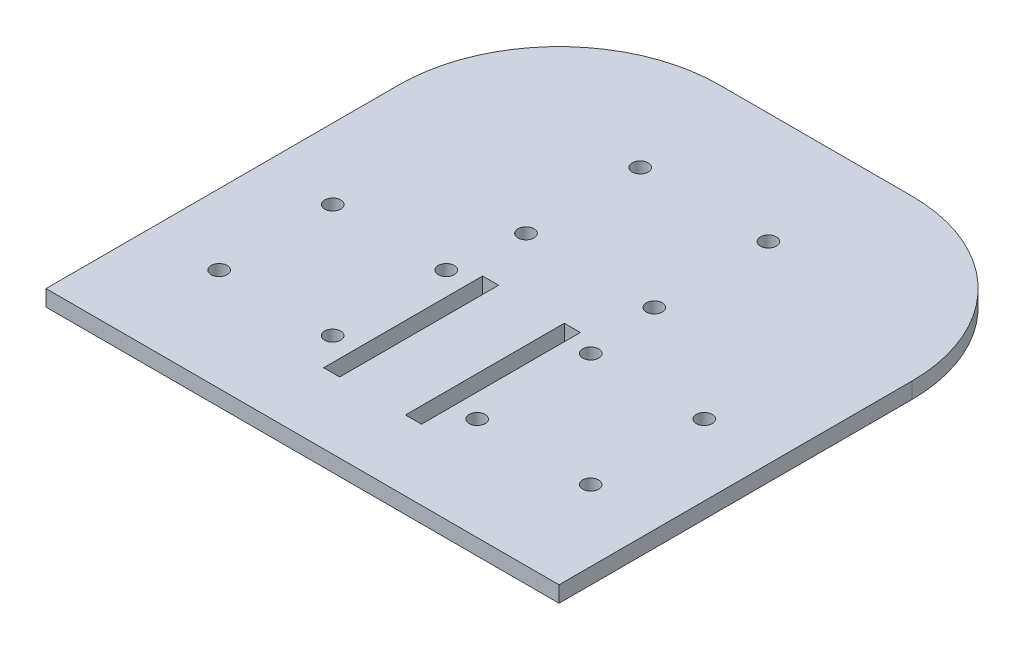
SolidWorks part; units mm, degrees
material "Acrylic (Medium-high impact)"
ref_plane "Front Plane" through (0, 0, 0) normal (0, 0, 1) x (1, 0, 0)
ref_plane "Top Plane" through (0, 0, 0) normal (0, 1, 0) x (1, 0, 0)
ref_plane "Right Plane" through (0, 0, 0) normal (1, 0, 0) x (0, 0, -1)
sketch "Sketch1" plane through (0, 0, 0) normal (0, 1, 0) x (1, 0, 0)
  line L1 (-101.6, -101.6) -> (101.6, -101.6)
  line L2 (-101.6, -101.6) -> (-101.6, 101.6)
  line L3 (-101.6, 101.6) -> (101.6, 101.6)
  line L4 (101.6, -101.6) -> (101.6, 101.6)
  line L5 (-101.6, -101.6) -> (101.6, 101.6) construction
  line L6 (-101.6, 101.6) -> (101.6, -101.6) construction
  point P0 (0, 0)
  dimension "D1" = 203.2
  dimension "D2" = 203.2
extrude "Boss-Extrude1" add sketch "Sketch1" along normal blind 6.35
sketch "Sketch2" plane through (0, 6.35, 0) normal (0, 1, 0) x (1, 0, 0)
  line L9 (101.6, 38.1) -> (101.6, 101.6)
  line L10 (101.6, 101.6) -> (38.1, 101.6)
  line L11 (-38.1, 101.6) -> (-101.6, 101.6)
  line L12 (-101.6, 101.6) -> (-101.6, 38.1)
  arc A2 (101.6, 38.1) -> (38.1, 101.6) centre (38.1, 38.1) ccw
  arc A3 (-101.6, 38.1) -> (-38.1, 101.6) centre (-38.1, 38.1) cw
extrude "Cut-Extrude1" cut sketch "Sketch2" against normal through all
sketch "Sketch9" plane through (0, 0, 0) normal (0, -1, 0) x (1, 0, 0)
  line L0 (-38.766, 10.8317) -> (-38.512, 10.8317) construction
  line L1 (-38.766, 73.756) -> (-38.512, 73.756) construction
  line L2 (38.5855, 10.8317) -> (38.3315, 10.8317) construction
  line L3 (-38.512, 10.8317) -> (-32.162, 10.8317)
  line L4 (-38.512, 10.8317) -> (-38.512, 73.756)
  line L5 (-38.512, 73.756) -> (-32.162, 73.756)
  line L6 (-32.162, 10.8317) -> (-32.162, 73.756)
  line L7 (38.5855, 73.756) -> (38.3315, 73.756) construction
  line L8 (-101.6, 101.6) -> (101.6, 101.6) construction
  line L13 (38.3315, 73.756) -> (31.9815, 73.756)
  line L14 (38.3315, 73.756) -> (38.3315, 10.8317)
  line L15 (38.3315, 10.8317) -> (31.9815, 10.8317)
  line L16 (31.9815, 73.756) -> (31.9815, 10.8317)
  line L17 (-101.6, -38.1) -> (-101.6, 101.6) construction
  circle A0 centre (-47.7463, 64.7757) radius 3.175 construction
  circle A1 centre (-47.7463, 19.812) radius 3.175 construction
  circle A2 centre (-92.71, 19.812) radius 3.175 construction
  circle A3 centre (-92.71, 64.7757) radius 3.175 construction
  circle A4 centre (-25.4903, -11.842) radius 3.175 construction
  circle A5 centre (25.3097, -11.842) radius 3.175 construction
  circle A6 centre (25.3097, -57.054) radius 3.175 construction
  circle A7 centre (-25.4903, -57.054) radius 3.175 construction
  circle A8 centre (47.5658, 19.812) radius 3.175 construction
  circle A9 centre (92.5295, 19.812) radius 3.175 construction
  circle A10 centre (92.5295, 64.7757) radius 3.175 construction
  circle A11 centre (47.5658, 64.7757) radius 3.175 construction
  circle A12 centre (-25.4903, -31.4508) radius 3.175
  circle A13 centre (25.3097, -31.4508) radius 3.175
  circle A14 centre (-25.4903, -76.6628) radius 3.175
  circle A15 centre (25.3097, -76.6628) radius 3.175
  circle A16 centre (-47.7463, 80.0157) radius 3.175
  circle A17 centre (-92.71, 80.0157) radius 3.175
  circle A18 centre (-47.7463, 35.052) radius 3.16
  circle A19 centre (-92.71, 35.052) radius 3.2058
  circle A20 centre (47.5658, 80.0157) radius 3.175
  circle A21 centre (92.5295, 80.0157) radius 3.175
  circle A22 centre (47.5658, 35.052) radius 3.175
  circle A23 centre (92.5295, 35.052) radius 3.175
  dimension "D22" = 6.35
  dimension "D23" = 6.35
  dimension "D24" = 6.35
  dimension "D26" = 6.35
  dimension "D27" = 6.35
  dimension "D28" = 6.35
  dimension "D29" = 6.35
  dimension "D30" = 6.35
  dimension "D31" = 6.35
  dimension "D32" = 6.35
  dimension "D33" = 6.35
  dimension "D36" = 19.6088
  dimension "D37" = 19.6088
  dimension "D38" = 19.6088
  dimension "D40" = 15.24
  dimension "D41" = 15.24
  dimension "D44" = 6.35
  dimension "D45" = 6.35
  dimension "D46" = 6.35
  dimension "D47" = 6.35
  dimension "D48" = 6.35
  dimension "D49" = 6.35
  dimension "D50" = 6.4115
  dimension "D51" = 6.32
  dimension "D1" = 0.254
  dimension "D2" = 6.35
  dimension "D4" = 44.9637
  dimension "D5" = 63.5883
  dimension "D6" = 44.9637
  dimension "D7" = 54.6863
  dimension "D8" = 53.944
  dimension "D9" = 60.548
  dimension "D10" = 135.86
  dimension "D11" = 141.9453
  dimension "D12" = 125.0145
  dimension "D13" = 131.2955
  dimension "D14" = 140.2758
  dimension "D15" = 185.2395
  dimension "D16" = 190.6185
  dimension "D17" = 122.191
  dimension "D18" = 74.2999
  dimension "D19" = 102.1121
  dimension "D20" = 140.8441
  dimension "D21" = 3.175
  dimension "D25" = 147.3059
  dimension "D34" = 8.89
  dimension "D35" = 81.788
  dimension "D39" = 19.6088
  dimension "D42" = 15.24
  dimension "D43" = 15.24
  dimension "D52" = 15.24
  dimension "D53" = 15.24
  dimension "D54" = 15.24
  dimension "D55" = 15.24
extrude "Cut-Extrude2" [suppressed] cut sketch "Sketch9" against normal through all
sketch "Sketch10" plane through (0, 0, 0) normal (0, -1, 0) x (1, 0, 0)
  line L0 (-19.462, 10.8317) -> (-13.112, 10.8317)
  line L1 (-13.112, 10.8317) -> (-13.112, 73.756)
  line L2 (-13.112, 73.756) -> (-19.462, 73.756)
  line L3 (-19.462, 73.756) -> (-19.462, 10.8317)
  line L4 (-38.512, 10.8317) -> (-32.162, 10.8317)
  line L5 (-32.162, 10.8317) -> (-32.162, 73.756)
  line L6 (-32.162, 73.756) -> (-38.512, 73.756)
  line L7 (-38.512, 73.756) -> (-38.512, 10.8317)
  line L8 (-38.512, 10.8317) -> (-32.162, 10.8317) construction
  line L9 (-32.162, 10.8317) -> (-32.162, 73.756) construction
  line L10 (-32.162, 73.756) -> (-38.512, 73.756) construction
  line L11 (-38.512, 73.756) -> (-38.512, 10.8317) construction
  line L12 (38.3315, 73.756) -> (31.9815, 73.756)
  line L13 (31.9815, 73.756) -> (31.9815, 10.8317)
  line L14 (31.9815, 10.8317) -> (38.3315, 10.8317)
  line L15 (38.3315, 10.8317) -> (38.3315, 73.756)
  line L16 (38.3315, 73.756) -> (31.9815, 73.756) construction
  line L17 (31.9815, 73.756) -> (31.9815, 10.8317) construction
  line L18 (31.9815, 10.8317) -> (38.3315, 10.8317) construction
  line L19 (38.3315, 10.8317) -> (38.3315, 73.756) construction
  line L20 (12.9315, 73.756) -> (19.2815, 73.756)
  line L21 (19.2815, 73.756) -> (19.2815, 10.8317)
  line L22 (19.2815, 10.8317) -> (12.9315, 10.8317)
  line L23 (12.9315, 10.8317) -> (12.9315, 73.756)
  circle A1 centre (25.3097, -31.4508) radius 3.175
  circle A2 centre (25.3097, -31.4508) radius 3.175 construction
  circle A3 centre (-25.4903, -31.4508) radius 3.175
  circle A4 centre (-25.4903, -31.4508) radius 3.175 construction
  circle A5 centre (25.3097, -76.6628) radius 3.175
  circle A6 centre (25.3097, -76.6628) radius 3.175 construction
  circle A7 centre (-25.4903, -76.6628) radius 3.175
  circle A8 centre (-25.4903, -76.6628) radius 3.175 construction
  circle A9 centre (-92.71, 80.0157) radius 3.175
  circle A10 centre (-92.71, 80.0157) radius 3.175 construction
  circle A11 centre (-47.7463, 80.0157) radius 3.175
  circle A12 centre (-47.7463, 80.0157) radius 3.175 construction
  circle A13 centre (92.5295, 35.052) radius 3.175
  circle A14 centre (92.5295, 35.052) radius 3.175 construction
  circle A15 centre (47.5658, 35.052) radius 3.175
  circle A16 centre (47.5658, 35.052) radius 3.175 construction
  circle A17 centre (92.5295, 80.0157) radius 3.175
  circle A18 centre (92.5295, 80.0157) radius 3.175 construction
  circle A19 centre (47.5658, 80.0157) radius 3.175
  circle A20 centre (47.5658, 80.0157) radius 3.175 construction
  circle A21 centre (-92.71, 35.052) radius 3.2058
  circle A22 centre (-92.71, 35.052) radius 3.2058 construction
  circle A23 centre (-47.7463, 35.052) radius 3.16
  circle A24 centre (-47.7463, 35.052) radius 3.16 construction
  circle A25 centre (-73.66, 80.0157) radius 3.175 construction
  circle A26 centre (-28.6963, 80.0157) radius 3.175 construction
  circle A27 centre (-73.66, 35.052) radius 3.175 construction
  circle A28 centre (-28.6963, 35.052) radius 3.175 construction
  circle A29 centre (28.5158, 80.0157) radius 3.175 construction
  circle A30 centre (73.4795, 80.0157) radius 3.175 construction
  circle A31 centre (73.4795, 35.052) radius 3.175 construction
  circle A32 centre (28.5158, 35.052) radius 3.175 construction
  circle A33 centre (25.3097, -12.4008) radius 3.175
  circle A34 centre (-25.4903, -12.4008) radius 3.175
  circle A35 centre (-25.4903, -57.6128) radius 3.175
  circle A36 centre (25.3097, -57.6128) radius 3.175
  circle A37 centre (-73.66, 16.002) radius 3.175
  circle A38 centre (-73.66, 60.9657) radius 3.175
  circle A39 centre (-28.6963, 60.9657) radius 3.175
  circle A40 centre (-28.6963, 16.002) radius 3.175
  circle A41 centre (28.5158, 60.9657) radius 3.175
  circle A42 centre (73.4795, 60.9657) radius 3.175
  circle A43 centre (73.4795, 16.002) radius 3.175
  circle A44 centre (28.5158, 16.002) radius 3.175
  dimension "D17" = 6.35
  dimension "D19" = 6.35
  dimension "D21" = 6.35
  dimension "D24" = 6.35
  dimension "D25" = 6.35
  dimension "D26" = 6.35
  dimension "D27" = 6.35
  dimension "D28" = 6.35
  dimension "D29" = 6.35
  dimension "D30" = 6.35
  dimension "D31" = 6.35
  dimension "D32" = 6.35
  dimension "D41" = 6.35
  dimension "D42" = 6.35
  dimension "D43" = 6.35
  dimension "D44" = 6.35
  dimension "D50" = 6.35
  dimension "D53" = 6.35
  dimension "D54" = 6.35
  dimension "D57" = 6.35
  dimension "D15" = 25.4
  dimension "D16" = 25.4
  dimension "D18" = 19.05
  dimension "D20" = 19.05
  dimension "D22" = 19.05
  dimension "D23" = 19.05
  dimension "D33" = 19.05
  dimension "D34" = 19.05
  dimension "D35" = 19.05
  dimension "D36" = 19.05
  dimension "D37" = 19.05
  dimension "D38" = 19.05
  dimension "D39" = 19.05
  dimension "D40" = 19.05
  dimension "D45" = 19.05
  dimension "D46" = 19.05
  dimension "D47" = 0
  dimension "D48" = 19.05
  dimension "D49" = 19.05
  dimension "D51" = 19.05
  dimension "D52" = 19.05
  dimension "D55" = 19.05
  dimension "D56" = 19.05
  dimension "D1" = 0
  dimension "D2" = 0
  dimension "D3" = 0
  dimension "D4" = 0
  dimension "D5" = 0
  dimension "D6" = 0
  dimension "D7" = 0
  dimension "D8" = 0
  dimension "D9" = 0
  dimension "D10" = 0
  dimension "D11" = 0
  dimension "D12" = 0
  dimension "D13" = 0
  dimension "D14" = 0
extrude "Cut-Extrude4" cut sketch "Sketch10" against normal through all
sketch "Sketch11" plane through (0, 0, 0) normal (0, -1, 0) x (1, 0, 0)
  line L0 (0, -101.6) -> (0, 101.6) construction
  line L1 (38.1, -101.6) -> (-38.1, -101.6) construction
  line L2 (-101.6, 101.6) -> (101.6, 101.6) construction
  line L3 (0, 0) -> (-33.8896, 19.5662) construction
  line L4 (0, 0) -> (55.2542, 31.901) construction
  line L18 (-73.66, 60.9657) -> (-28.6963, 60.9657)
  line L19 (-73.66, 60.9657) -> (-73.66, 16.002)
  line L20 (-73.66, 16.002) -> (-28.6963, 16.002)
  line L21 (-28.6963, 60.9657) -> (-28.6963, 16.002)
  line L22 (28.5158, 60.9657) -> (73.4795, 60.9657)
  line L23 (28.5158, 60.9657) -> (28.5158, 16.002)
  line L24 (28.5158, 16.002) -> (73.4795, 16.002)
  line L25 (73.4795, 60.9657) -> (73.4795, 16.002)
  dimension "D3" = 60
  dimension "D1" = 0
  dimension "D2" = 0
  dimension "D4" = 30
  dimension "D5" = 60
  dimension "D6" = 30
sketch "Sketch12" plane through (0, 0, 0) normal (0, -1, 0) x (1, 0, 0)
  line L0 (-101.6, 101.6) -> (-101.6, -38.1)
  line L1 (-101.6, 101.6) -> (101.6, 101.6)
  line L2 (101.6, 101.6) -> (101.6, -38.1)
  line L3 (-38.1, -101.6) -> (38.1, -101.6)
  arc A0 (38.1, -101.6) -> (101.6, -38.1) centre (38.1, -38.1) ccw
  arc A1 (-101.6, -38.1) -> (-38.1, -101.6) centre (-38.1, -38.1) ccw
